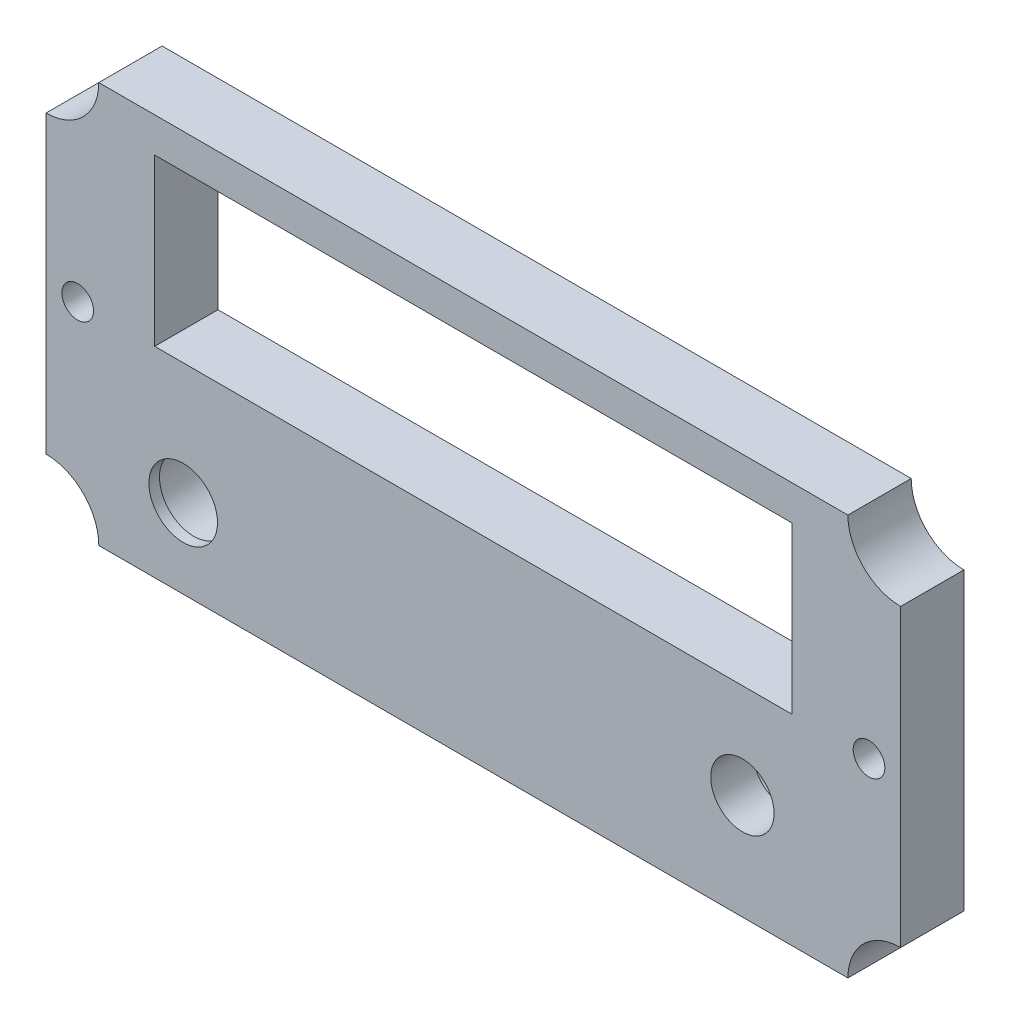
SolidWorks part; units mm, degrees
ref_plane "Front Plane" through (0, 0, 0) normal (0, 0, 1) x (1, 0, 0)
ref_plane "Top Plane" through (0, 0, 0) normal (0, 1, 0) x (1, 0, 0)
ref_plane "Right Plane" through (0, 0, 0) normal (1, 0, 0) x (0, 0, -1)
sketch "Sketch1" plane through (0, 0, 0) normal (0, 0, 1) x (1, 0, 0)
  line L0 (-35.5, 19) -> (35.5, 19)
  line L1 (-40.5, 14) -> (-40.5, -14)
  line L2 (-35.5, -19) -> (35.5, -19)
  line L3 (40.5, 14) -> (40.5, -14)
  line L4 (0, 29.5031) -> (0, -29.5031) construction
  line L5 (-52.4324, 0) -> (52.4324, 0) construction
  arc A0 (-40.5, 14) -> (-35.5, 19) centre (-40.5, 19) ccw
  arc A1 (-40.5, -14) -> (-35.5, -19) centre (-40.5, -19) cw
  arc A2 (40.5, -14) -> (35.5, -19) centre (40.5, -19) ccw
  arc A3 (40.5, 14) -> (35.5, 19) centre (40.5, 19) cw
  dimension "D1" = 10
  dimension "D6" = 5
  dimension "D2" = 81
  dimension "D3" = 40.5
  dimension "D4" = 38
  dimension "D5" = 19
  dimension "D7" = 5
extrude "Base" add sketch "Sketch1" along normal blind 6
sketch "Sketch2" plane through (0, 0, 6) normal (0, 0, 1) x (1, 0, 0)
  line L0 (0, 21.9217) -> (0, -30.7411) construction
  line L1 (35.5, 19) -> (-35.5, 19) construction
  line L2 (-40.5, 14) -> (-40.5, -14) construction
  circle A0 centre (-37.5, 0) radius 1.5
  circle A1 centre (37.5, 0) radius 1.5
  dimension "D1" = 3
  dimension "D2" = 0
  dimension "D3" = 19
  dimension "D4" = 3
extrude "Screws Cut" cut sketch "Sketch2" against normal through all both and the other way through all
sketch "Sketch4" plane through (0, 0, 6) normal (0, 0, 1) x (1, 0, 0)
  line L0 (-30.2, 15.7) -> (30.2, 15.7)
  line L1 (-30.2, 15.7) -> (-30.2, 0)
  line L2 (-30.2, 0) -> (30.2, 0)
  line L3 (30.2, 15.7) -> (30.2, 0)
  line L4 (-40.5, 14) -> (-40.5, -14) construction
  dimension "D1" = 60.4
  dimension "D2" = 15.7
  dimension "D3" = 0
  dimension "D4" = 10.3
extrude "LCD Cut" cut sketch "Sketch4" against normal through all both
sketch "Sketch5" plane through (0, 0, 6) normal (0, 0, 1) x (1, 0, 0)
  line L1 (-40.5, 14) -> (-40.5, -14) construction
  line L2 (-35.5, -19) -> (35.5, -19) construction
  circle A0 centre (-27.5, -11.5) radius 3.75
  dimension "D1" = 7.5
  dimension "D3" = 13
  dimension "D4" = 7.5
extrude "TestButton Big Cut" cut sketch "Sketch5" against normal through all both
sketch "Sketch6" plane through (0, 0, 6) normal (0, 0, 1) x (1, 0, 0)
  circle A0 centre (-27.5, -11.5) radius 3.25
  circle A1 centre (-27.5, -11.5) radius 4
  dimension "D1" = 6.5
  dimension "D2" = 8
extrude "TestButton Piece Maintainer" add sketch "Sketch6" against normal blind 1
sketch "Sketch7" plane through (0, 0, 6) normal (0, 0, 1) x (1, 0, 0)
  line L0 (-35.5, -19) -> (35.5, -19) construction
  line L1 (40.5, -14) -> (40.5, 14) construction
  circle A0 centre (25.5, -9) radius 3.425
  dimension "D1" = 6.85
  dimension "D2" = 10
  dimension "D3" = 15
extrude "Brightness Cut" cut sketch "Sketch7" against normal through all both and the other way through all
sketch "Sketch8" plane through (0, 0, 6) normal (0, 0, 1) x (1, 0, 0)
  circle A0 centre (25.5, -9) radius 3
  circle A1 centre (25.5, -9) radius 3.5
  dimension "D1" = 7
  dimension "D2" = 6
extrude "Brightness Back Cut" add sketch "Sketch8" against normal blind 4
